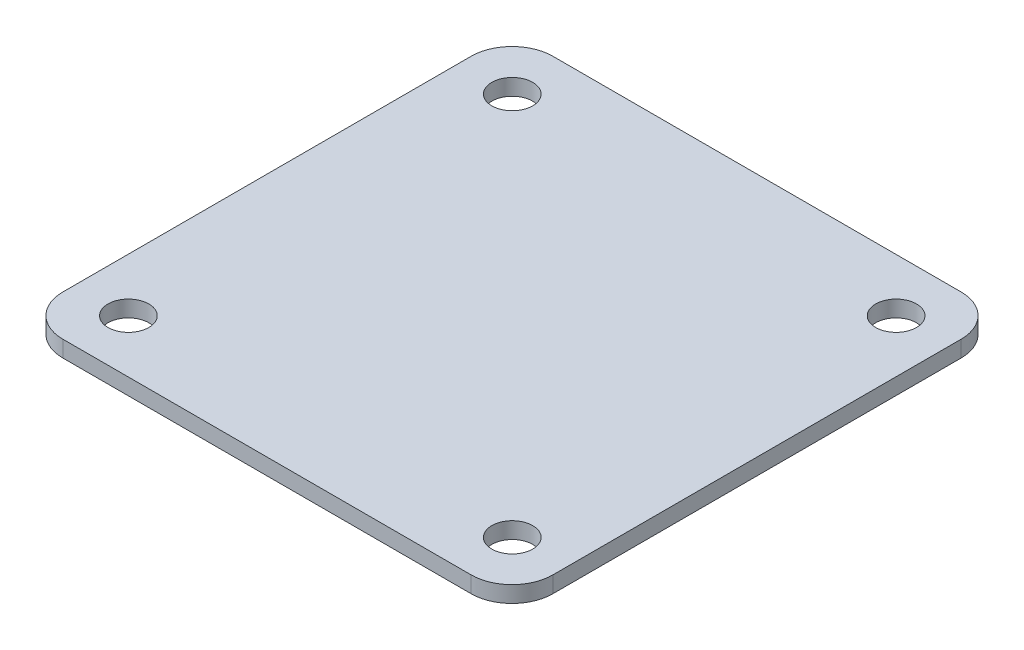
SolidWorks part; units mm, degrees
ref_plane "Front" through (0, 0, 0) normal (0, 0, 1) x (1, 0, 0)
ref_plane "Top" through (0, 0, 0) normal (0, 1, 0) x (1, 0, 0)
ref_plane "Right" through (0, 0, 0) normal (1, 0, 0) x (0, 0, -1)
sketch "Sketch1" plane through (0, 0, 0) normal (0, 1, 0) x (1, 0, 0)
  line L0 (26.2716, -11.9169) -> (-33.7284, -11.9169) construction
  line L1 (-33.7284, 18.0831) -> (26.2716, 18.0831)
  line L2 (-33.7284, 18.0831) -> (-33.7284, -41.9169)
  line L3 (-33.7284, -41.9169) -> (26.2716, -41.9169)
  line L4 (26.2716, 18.0831) -> (26.2716, -41.9169)
  circle A0 centre (19.8025, 11.5831) radius 2.5
  circle A1 centre (-27.1975, 11.5831) radius 2.5
  circle A2 centre (19.8025, -35.4169) radius 2.5
  circle A3 centre (-27.1975, -35.4169) radius 2.5
  dimension "D3" = 47
  dimension "D1" = 60
  dimension "D2" = 60
  dimension "D4" = 23.5
extrude "Boss-Extrude1" add sketch "Sketch1" along normal blind 2
fillet "Fillet1" radius 5 4 edges at (-33.7284, 1, 41.9169) (-33.7284, 1, -18.0831) (26.2716, 1, -18.0831) (26.2716, 1, 41.9169)
